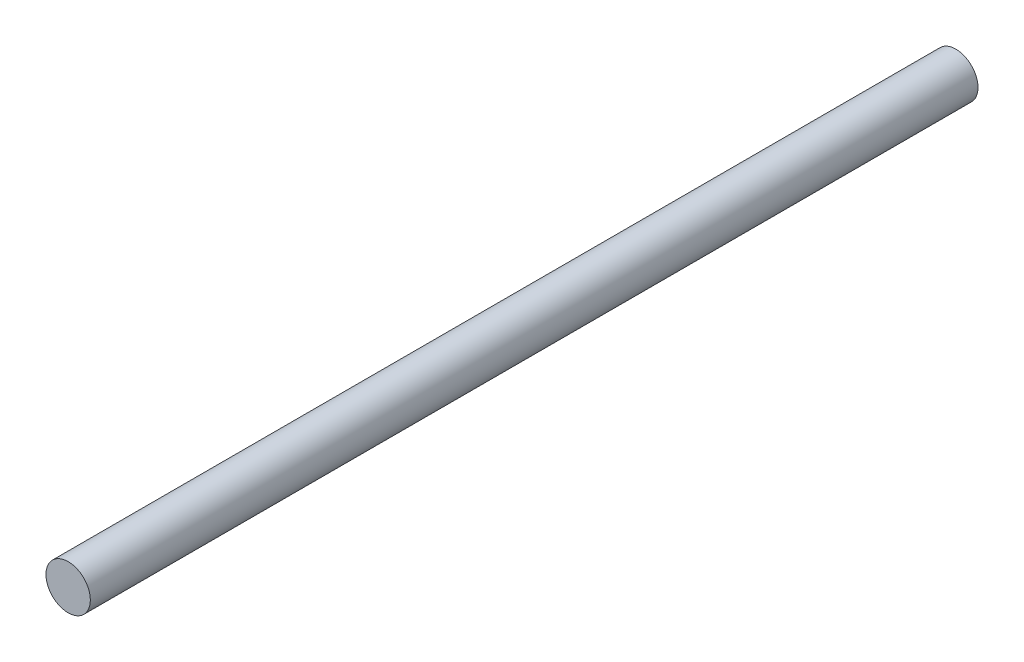
SolidWorks part; units mm, degrees
ref_plane "Front Plane" through (0, 0, 0) normal (0, 0, 1) x (1, 0, 0)
ref_plane "Top Plane" through (0, 0, 0) normal (0, 1, 0) x (1, 0, 0)
ref_plane "Right Plane" through (0, 0, 0) normal (1, 0, 0) x (0, 0, -1)
sketch "Sketch1" plane through (0, 0, 0) normal (0, 0, 1) x (1, 0, 0)
  circle A0 centre (0, 0) radius 0.7938
  dimension "D1" = 1.5875
extrude "Boss-Extrude1" add sketch "Sketch1" along normal blind 31.75
